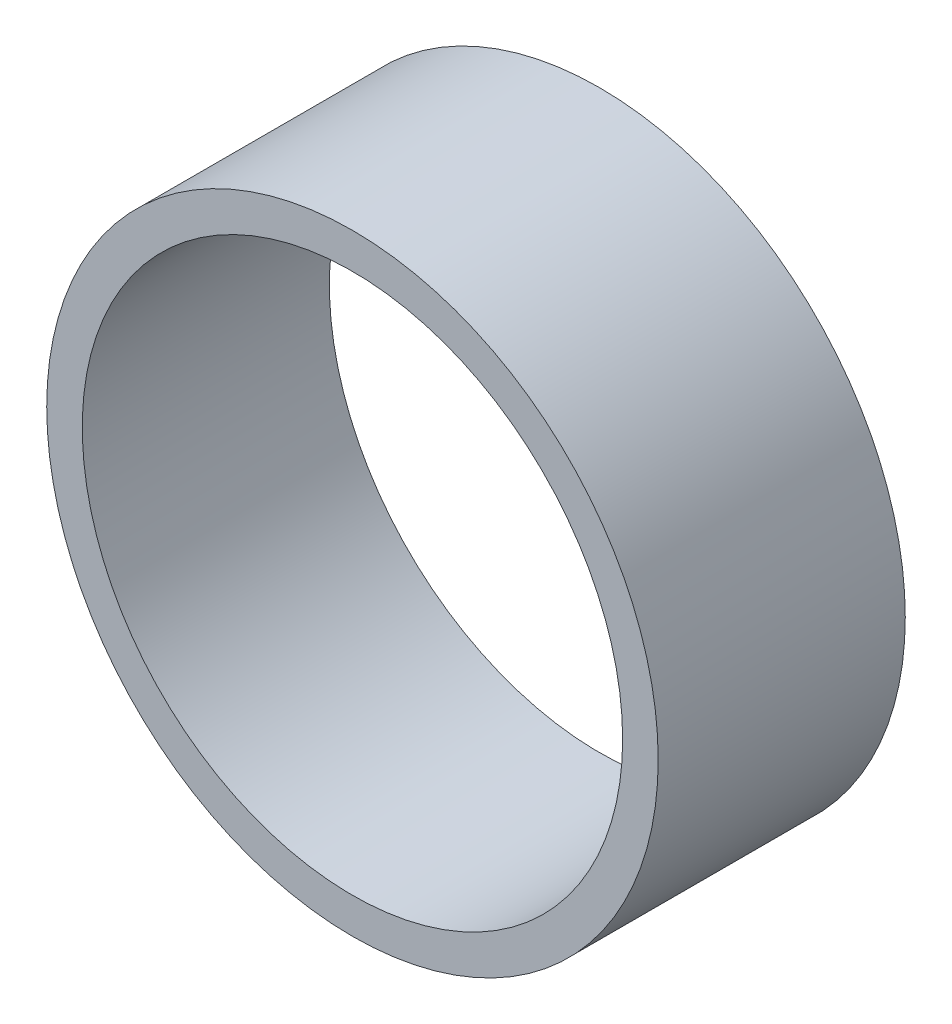
SolidWorks part; units mm, degrees
material "Silicon"
ref_plane "Front" through (0, 0, 0) normal (0, 0, 1) x (1, 0, 0)
ref_plane "Top" through (0, 0, 0) normal (0, 1, 0) x (1, 0, 0)
ref_plane "Right" through (0, 0, 0) normal (1, 0, 0) x (0, 0, -1)
sketch "Sketch1" plane through (0, 0, 0) normal (0, 0, 1) x (1, 0, 0)
  circle A0 centre (0, 0) radius 86
  circle A1 centre (0, 0) radius 76
extrude "Boss-Extrude1" add sketch "Sketch1" along normal blind 69.5
